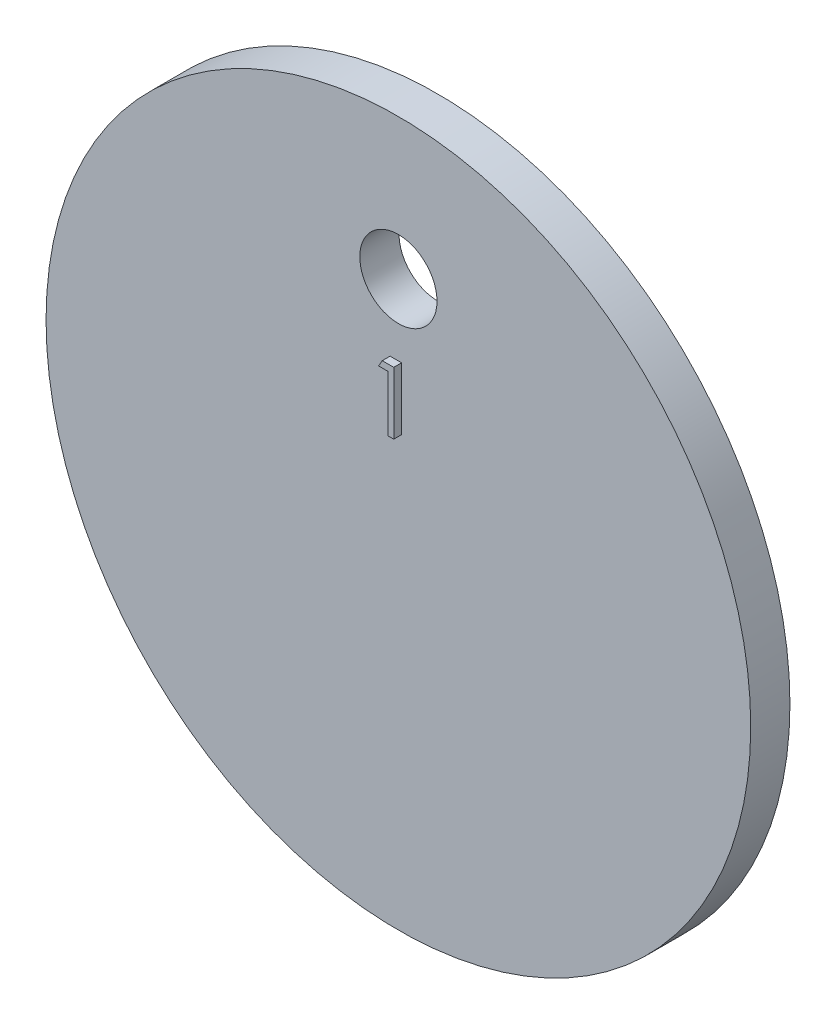
SolidWorks part; units mm, degrees
ref_plane "Ebene vorne" through (0, 0, 0) normal (0, 0, 1) x (1, 0, 0)
ref_plane "Ebene oben" through (0, 0, 0) normal (0, 1, 0) x (1, 0, 0)
ref_plane "Ebene rechts" through (0, 0, 0) normal (1, 0, 0) x (0, 0, -1)
sketch "Skizze1" plane through (0, 0, 0) normal (0, 0, 1) x (1, 0, 0)
  circle A0 centre (0, 0) radius 44.9441
  circle A1 centre (0, 26.9875) radius 4.9237
extrude "Aufsatz-Linear austragen1" add sketch "Skizze1" along normal blind 5
sketch "Skizze2" plane through (0, 0, 5) normal (0, 0, 1) x (1, 0, 0)
  line L0 (-6.1143, 10) -> (6.1143, 10) construction
  line L1 (0, 0) -> (0, 10) construction
  text T0 "1" font "Century Gothic" height in points 30
  dimension "D1" = 10
extrude "Aufsatz-Linear austragen2" add sketch "Skizze2" along normal blind 1
